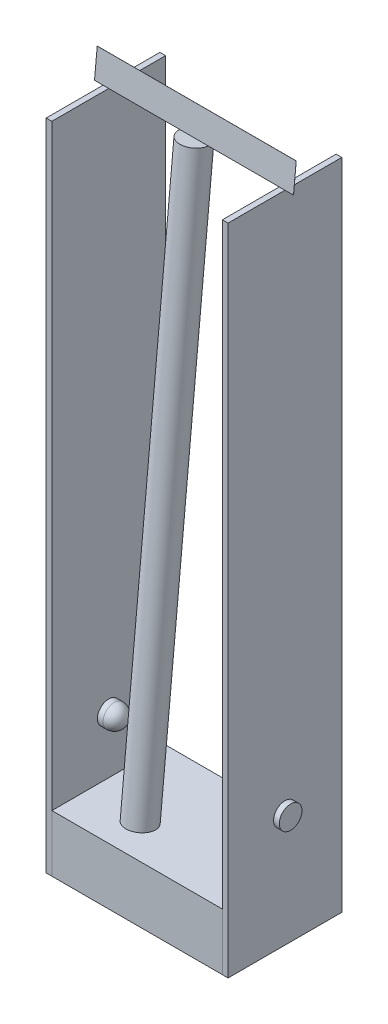
SolidWorks part; units mm, degrees
ref_plane "Front Plane" through (0, 0, 0) normal (0, 0, 1) x (1, 0, 0)
ref_plane "Top Plane" through (0, 0, 0) normal (0, 1, 0) x (1, 0, 0)
ref_plane "Right Plane" through (0, 0, 0) normal (1, 0, 0) x (0, 0, -1)
sketch "Sketch1" plane through (0, 0, 0) normal (0, 1, 0) x (1, 0, 0)
  line L1 (-15, 10) -> (15, 10)
  line L2 (-15, 10) -> (-15, -10)
  line L3 (-15, -10) -> (15, -10)
  line L4 (15, 10) -> (15, -10)
  line L5 (-15, 10) -> (15, -10) construction
  line L6 (-15, -10) -> (15, 10) construction
  point P0 (0, 0)
  dimension "D1" = 20
  dimension "D2" = 30
extrude "Boss-Extrude1" add sketch "Sketch1" along normal blind 10
sketch "Sketch2" plane through (-15, 0, 0) normal (-1, 0, 0) x (0, 0, 1)
  line L0 (-10, 0) -> (10, 0)
  line L1 (-10, 0) -> (-10, 115)
  line L2 (10, 0) -> (10, 115)
  line L3 (-10, 115) -> (10, 115)
  dimension "D1" = 115
extrude "Boss-Extrude2" add sketch "Sketch2" along normal blind 1 separate body
sketch "Sketch3" plane through (-16, 0, 0) normal (-1, 0, 0) x (0, 0, 1)
  line L0 (10, 115) -> (-10, 115) construction
  circle A0 centre (0, 20) radius 2
  point P4 (0, 25)
  point P5 (0, 0)
  dimension "D2" = 4
  dimension "D1" = 95
extrude "Boss-Extrude6" add sketch "Sketch3" along normal blind 1 and the other way blind 4 separate body
fillet "Fillet1" radius 2 1 edges at (-12, 20, 2)
mirror "Mirror3" about plane through (0, 0, 0) normal (1, 0, 0) of bodies 102 110
sketch "Sketch5" plane through (0, 115, 0) normal (0, 1, 0) x (1, 0, 0)
  line L0 (-15, 10) -> (-15, -10) construction
  line L1 (-15, 0) -> (15, 0) construction
  line L2 (15, -10) -> (15, 10) construction
  point P0 (-15, 0)
ref_plane "Plane2" through (0, 1.0337, 10.8539) normal (0, -0.0948, -0.9955) x (-1, 0, 0)
sketch "Sketch6" plane through (0, 1.0337, 10.8539) normal (0, -0.0948, -0.9955) x (-1, 0, 0)
  line L0 (-17.5, 114.482) -> (17.5, 114.482)
  line L1 (-17.5, 114.482) -> (-17.5, 119.482)
  line L2 (17.5, 114.482) -> (17.5, 119.482)
  line L3 (-17.5, 119.482) -> (17.5, 119.482)
  line L4 (15, 114.482) -> (-15, 114.482) construction
  line L5 (-17.5, 114.482) -> (17.5, 119.482) construction
  point P6 (0, 116.982)
  point P7 (0, 0)
  point P8 (0, 0)
  point P9 (0, 0)
  point P10 (0, 0)
  dimension "D1" = 5
  dimension "D2" = 35
extrude "Boss-Extrude3" add sketch "Sketch6" along normal blind 0.01 separate body contours L2 L3 L1 L0
sketch "Sketch7" plane through (0, 113.9663, -10.8539) normal (0, -0.9955, 0.0948) x (1, 0, 0)
  line L0 (17.5, 10.893) -> (-17.5, 10.893) construction
  circle A0 centre (0, 10.893) radius 2.5
  point P2 (1.5616, 10.8587)
  dimension "D1" = 5
extrude "Boss-Extrude5" add sketch "Sketch7" along normal blind 100
sketch "Sketch8" plane through (-16, 0, 0) normal (-1, 0, 0) x (0, 0, 1)
  circle A0 centre (0, 20) radius 2
  point P3 (0, 20)
  point P4 (0, 20)
  point P5 (0, 20)
  dimension "D1" = 4
extrude "Cut-Extrude2" cut sketch "Sketch8" against normal through all both and the other way through all
